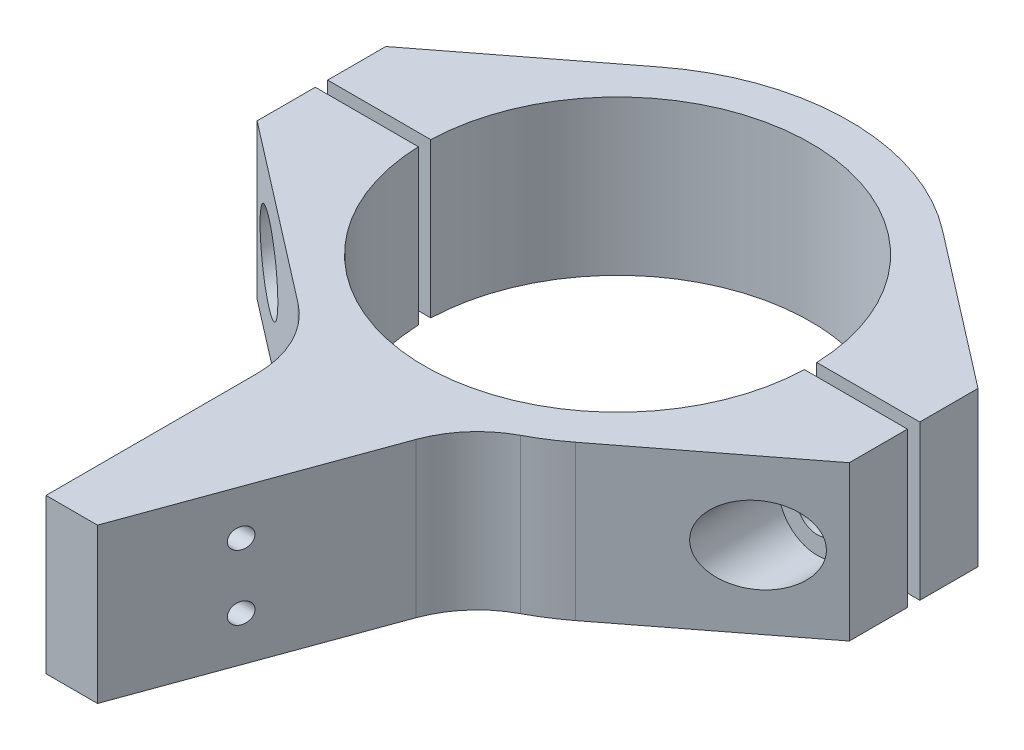
SolidWorks part; units mm, degrees
material "PET"
ref_plane "Front" through (0, 0, 0) normal (0, 0, 1) x (1, 0, 0)
ref_plane "Top" through (0, 0, 0) normal (0, 1, 0) x (1, 0, 0)
ref_plane "Right" through (0, 0, 0) normal (1, 0, 0) x (0, 0, -1)
sketch "Sketch1" plane through (0, 0, 0) normal (0, 1, 0) x (1, 0, 0)
  circle A0 centre (0, 0) radius 23.8125
  circle A1 centre (0, 0) radius 28.575
  point P6 (-28.5366, 1.4813)
  dimension "D1" = 47.625
  dimension "D2" = 57.15
extrude "Boss-Extrude1" add sketch "Sketch1" along normal mid plane 19.05
sketch "Sketch2" plane through (0, 9.525, 0) normal (0, 1, 0) x (1, 0, 0)
  line L0 (-17.4427, 22.6337) -> (-36.5125, 7.9375)
  line L1 (-36.5125, 7.9375) -> (-36.5125, -7.9375)
  line L2 (-36.5125, -7.9375) -> (-17.4427, -22.6337)
  line L3 (0, 0) -> (0, 8.5819) construction
  line L4 (36.5125, -7.9375) -> (17.4427, -22.6337)
  line L5 (36.5125, 7.9375) -> (36.5125, -7.9375)
  line L6 (17.4427, 22.6337) -> (36.5125, 7.9375)
  circle A0 centre (0, 0) radius 28.575 construction
  circle A2 centre (0, 0) radius 23.8125 construction
  arc A3 (-17.4427, 22.6337) -> (-17.4427, -22.6337) centre (0, 0) ccw
  arc A4 (17.4427, 22.6337) -> (17.4427, -22.6337) centre (0, 0) cw
  point P8 (-36.5125, 0)
  dimension "D1" = 15.875
  dimension "D2" = 12.7
extrude "Boss-Extrude2" add sketch "Sketch2" against normal up to surface (19.05 mm away) up to face at (0, -9.525, 28.575)
sketch "Sketch3" plane through (0, 9.525, 0) normal (0, 1, 0) x (1, 0, 0)
  line L0 (-36.5125, 7.9375) -> (-36.5125, -7.9375) construction
  line L1 (-36.5125, 0.762) -> (36.5125, 0.762)
  line L2 (-36.5125, 0.762) -> (-36.5125, -0.762)
  line L3 (-36.5125, -0.762) -> (36.5125, -0.762)
  line L4 (36.5125, 0.762) -> (36.5125, -0.762)
  line L5 (36.5125, -7.9375) -> (36.5125, 7.9375) construction
  line L6 (-36.5125, 0.762) -> (36.5125, -0.762) construction
  dimension "D1" = 1.524
extrude "Cut-Extrude1" cut sketch "Sketch3" against normal through all and the other way through all
sketch "Sketch4" plane through (0, 0, 0) normal (0, 1, 0) x (1, 0, 0)
  line L0 (-27.6037, -0.762) -> (-27.6037, -5.5245)
  line L1 (-36.5125, -0.762) -> (-23.8003, -0.762) construction
  line L2 (-27.6037, -5.5245) -> (-25.3939, -5.5245)
  line L3 (-25.3939, -5.5245) -> (-25.3939, -16.5061)
  line L4 (-36.5125, -7.9375) -> (-17.4427, -22.6337) construction
  line L5 (-26.9814, 0.762) -> (-26.9814, 15.2827)
  line L6 (-23.8003, 0.762) -> (-36.5125, 0.762) construction
  line L7 (-17.4427, 22.6337) -> (-36.5125, 7.9375) construction
  line L8 (-26.9814, 15.2827) -> (-30.1564, 15.2827)
  line L9 (-30.1564, 15.2827) -> (-30.1564, -16.5061)
  line L10 (-30.1564, -16.5061) -> (-25.3939, -16.5061)
  line L11 (-26.9814, 0.762) -> (-27.6037, -0.762)
  line L12 (-30.1564, 15.2827) -> (-30.1564, 20.5845) construction
  point P14 (0, 0)
  point P18 (-31.8251, -15.2201)
  point P19 (-30.1564, -0.762)
  point P20 (-30.1564, 20.5845)
  dimension "D1" = 5.1054
  dimension "D2" = 9.525
  dimension "D3" = 6.35
  dimension "D4" = 4.7625
revolve "Cut-Revolve1" cut sketch "Sketch4" angle 360 about L12
mirror "Mirror1" about plane through (0, 0, 0) normal (1, 0, 0) of "Cut-Revolve1"
sketch "Sketch5" plane through (0, 9.525, 0) normal (0, 1, 0) x (1, 0, 0)
  line L0 (9.1612, -27.0667) -> (-3.175, -60.96)
  line L2 (-3.175, -60.96) -> (-9.525, -60.96)
  line L5 (-9.525, -60.96) -> (-9.525, -34.9819)
  line L11 (-23.8003, -0.762) -> (-36.5125, -0.762)
  line L12 (-36.5125, -0.762) -> (-36.5125, -7.9375)
  line L13 (-36.5125, -7.9375) -> (-17.4427, -22.6337)
  line L14 (17.4427, -22.6337) -> (36.5125, -7.9375)
  line L15 (36.5125, -7.9375) -> (36.5125, -0.762)
  line L16 (36.5125, -0.762) -> (23.8003, -0.762)
  line L19 (-14.4727, -24.9225) -> (-17.4427, -22.6337)
  arc A0 (-17.4427, -22.6337) -> (17.4427, -22.6337) centre (0, 0) ccw construction
  arc A2 (-9.525, -34.9819) -> (-14.4727, -24.9225) centre (-22.225, -34.9819) ccw
  arc A3 (-17.4427, -22.6337) -> (17.4427, -22.6337) centre (0, 0) ccw
  arc A4 (-23.8003, -0.762) -> (23.8003, -0.762) centre (0, 0) ccw
  arc A5 (-17.4427, -22.6337) -> (9.1612, -27.0667) centre (0, 0) ccw
  point P1 (0, -63.5)
  point P10 (0, 0)
  point P16 (13.0958, -25.3974)
  point P17 (-11.4686, -27.2376)
  dimension "D6" = 12.7
  dimension "D2" = 20
  dimension "D3" = 60.96
  dimension "D4" = 9.525
  dimension "D5" = 6.35
  dimension "D1" = 0
extrude "Boss-Extrude3" add sketch "Sketch5" against normal up to surface (19.05 mm away) up to face at (0, -9.525, 11.6478)
sketch "Sketch9" plane through (-9.525, 0, 0) normal (1, 0, 0) x (0, 0, -1)
  line L0 (-60.96, 9.525) -> (-47.971, 4) construction
  line L3 (-47.971, -4) -> (-34.9819, -9.525) construction
  point P0 (-47.971, 4)
  point P2 (-47.971, -4)
  point P15 (0, 0)
  point P16 (-63.5, 13.2477)
  point P17 (-63.5, 12.7)
  point P19 (0, 0)
  point P20 (-37.7642, -12.7)
  dimension "D1" = 8
hole_wizard "M3x0.5 Tapped Hole1" positions "Sketch9" profile "Sketch8" tap size "M3x0.5" standard "ANSI Metric" end condition through all
sketch "Sketch8" plane through (-9.525, 4, 47.971) normal (0, 1, 0) x (0, 0, 1)
  line L0 (0, 0) -> (0, 46.0375)
  line L1 (0, 46.0375) -> (1.25, 46.0375)
  line L2 (1.25, 46.0375) -> (1.25, 0)
  line L5 (1.25, 0) -> (0, 0)
  line L11 (0, -6.35) -> (0, 107.95) construction
  dimension "Thru Tap Drill Dia." = 2.5
  dimension "Thru Tap Drill Depth" = 46.0375
cosmetic thread "Hole Thread1" parameters "D2"=3
cosmetic thread "Hole Thread2" parameters "D2"=3
fillet "Fillet1" radius 12.7 1 edges at (9.1612, 0, 27.0667)
